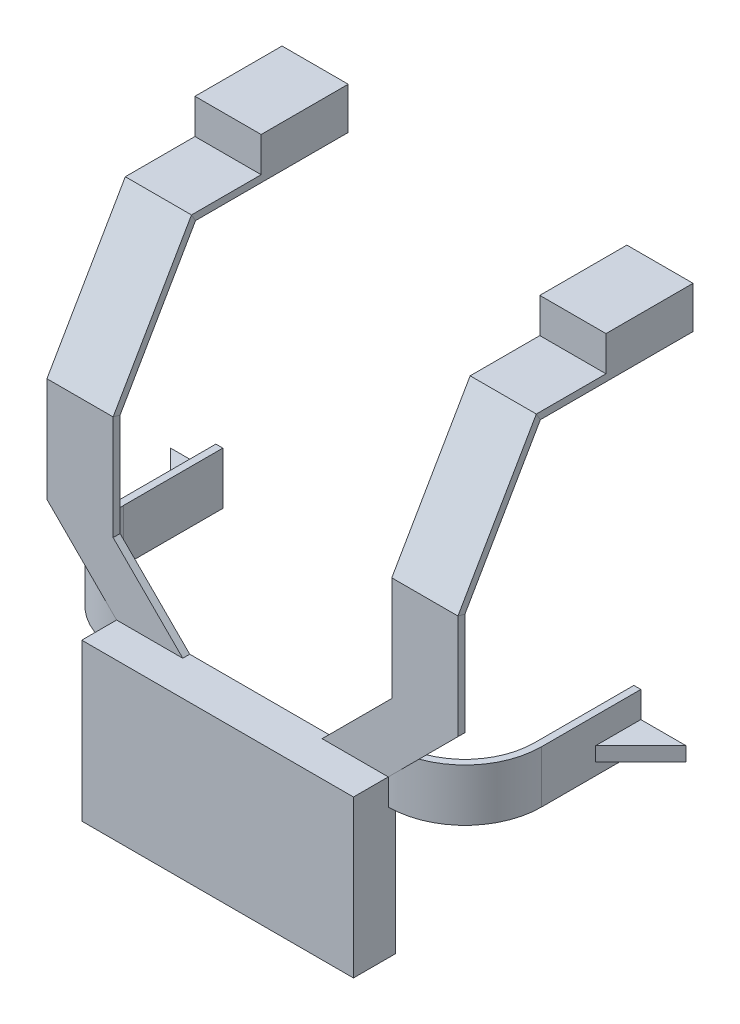
SolidWorks part; units mm, degrees
ref_plane "Front" through (0, 0, 0) normal (0, 0, 1) x (1, 0, 0)
ref_plane "Top" through (0, 0, 0) normal (0, 1, 0) x (1, 0, 0)
ref_plane "Right" through (0, 0, 0) normal (1, 0, 0) x (0, 0, -1)
sketch "草图1" plane through (0, 0, 0) normal (0, 0, 1) x (1, 0, 0)
  line L1 (0, 0) -> (0, -101.6526) construction
  line L2 (-40, 0) -> (40, 0)
  line L4 (-78, 0) -> (-78, 50)
  line L5 (-40, 50) -> (40, 50)
  line L6 (78, 0) -> (78, 50)
  line L8 (-78, 0) -> (-78, -160)
  line L9 (-78, -160) -> (-40, -160)
  line L10 (-40, 0) -> (-40, -160)
  line L12 (78, 0) -> (78, -160)
  line L13 (78, -160) -> (40, -160)
  line L14 (40, 0) -> (40, -160)
  line L15 (-143.4043, 90) -> (126.5484, 90) construction
  line L16 (-78, 50) -> (-118, 90)
  line L17 (-118, 90) -> (-80, 90)
  line L18 (-80, 90) -> (-40, 50)
  line L19 (78, 50) -> (118, 90)
  line L20 (118, 90) -> (80, 90)
  line L21 (80, 90) -> (40, 50)
  dimension "D1" = 156
  dimension "D2" = 78
  dimension "D3" = 50
  dimension "D4" = 160
  dimension "D5" = 38
  dimension "D6" = 38
  dimension "D7" = 40
  dimension "D8" = 38
  dimension "D9" = 38
extrude "凸台-拉伸1" add sketch "草图1" along normal blind 4
sketch "草图11" plane through (0, 0, 4) normal (0, 0, 1) x (1, 0, 0)
  line L0 (78, -160) -> (78, 50) construction
  line L1 (-78, 50) -> (78, 50)
  line L2 (-78, 50) -> (-78, -40)
  line L3 (-78, -40) -> (78, -40)
  line L4 (78, 50) -> (78, -40)
  dimension "D1" = 90
extrude "凸台-拉伸2" add sketch "草图11" along normal blind 20
sketch "草图12" plane through (0, 90, 0) normal (0, 1, 0) x (1, 0, 0)
  line L1 (-118, 0) -> (-80, 0)
  line L2 (-118, 0) -> (-118, -4)
  line L3 (-118, -4) -> (-80, -4)
  line L4 (-80, 0) -> (-80, -4)
  line L5 (118, 0) -> (80, 0)
  line L6 (118, 0) -> (118, -4)
  line L7 (118, -4) -> (80, -4)
  line L8 (80, 0) -> (80, -4)
sketch "草图13" plane through (78, 0, 0) normal (1, 0, 0) x (0, 0, -1)
  line L0 (-4, 90) -> (-4, 150)
  line L3 (-4, 150) -> (41, 227.9423)
  line L4 (41, 227.9423) -> (131, 227.9423)
  dimension "D1" = 60
  dimension "D2" = 150
  dimension "D3" = 90
  dimension "D5" = 90
sweep "扫描1" add profiles "草图12" path "草图13"
sketch "草图14" plane through (0, 227.9423, 0) normal (0, 1, 0) x (1, 0, 0)
  line L0 (-80, 41) -> (-80, 131) construction
  line L1 (-118, 131) -> (-80, 131)
  line L2 (-118, 131) -> (-118, 81)
  line L3 (-118, 81) -> (-80, 81)
  line L4 (-80, 131) -> (-80, 81)
  line L5 (80, 41) -> (80, 131) construction
  line L6 (118, 131) -> (80, 131)
  line L7 (118, 131) -> (118, 81)
  line L8 (118, 81) -> (80, 81)
  line L9 (80, 131) -> (80, 81)
  dimension "D1" = 50
  dimension "D2" = 50
extrude "凸台-拉伸3" add sketch "草图14" along normal blind 20
sketch "草图16" plane through (0, 0, 0) normal (0, 0, -1) x (-1, 0, 0)
  line L0 (15.8437, -40) -> (-148.9308, -40) construction
  line L1 (40, -40) -> (-40, -40) construction
  line L3 (-110.3778, -40) -> (127.8058, -40)
  line L4 (-110.3778, -40) -> (-110.3778, -172.2953)
  line L5 (-110.3778, -172.2953) -> (127.8058, -172.2953)
  line L6 (127.8058, -40) -> (127.8058, -172.2953)
extrude "切除-拉伸1" cut sketch "草图16" against normal blind 10
sketch "草图17" plane through (0, -40, 0) normal (0, -1, 0) x (1, 0, 0)
  line L0 (0, 0) -> (0, 25.1207) construction
  line L1 (-20, 0) -> (20, 0)
  line L2 (-20, 0) -> (-20, 20)
  line L3 (-20, 20) -> (20, 20)
  line L4 (20, 0) -> (20, 20)
  dimension "D1" = 40
  dimension "D2" = 20
  dimension "D3" = 20
extrude "凸台-拉伸4" add sketch "草图17" along normal blind 4
sketch "草图21" plane through (0, -44, 0) normal (0, -1, 0) x (1, 0, 0)
  line L0 (-20, 0) -> (20, 0) construction
  circle A0 centre (0, 9.5) radius 6
  circle A1 centre (0, 9.5) radius 4
  dimension "D1" = 9.5
extrude "凸台-拉伸8" add sketch "草图21" along normal blind 4
sketch "草图28" plane through (0, 50, 0) normal (0, 1, 0) x (1, 0, 0)
  line L0 (-78, -4) -> (-78, 0) construction
  line L1 (-40, -4) -> (-80, -4) construction
  line L2 (-78, -24) -> (-78, -4) construction
  line L3 (-40, 0) -> (-80, 0) construction
  line L4 (-118, 97) -> (-118, -25.7453) construction
  line L7 (-78, 0) -> (-126.1781, 48.1781) construction
  line L8 (-122, 40) -> (-122, 97)
  line L9 (-122, 97) -> (-118, 97)
  line L10 (-118, 97) -> (-118, 40)
  line L11 (-78, -4) -> (-78, 0)
  line L12 (78, -4) -> (78, 102.1257) construction
  line L13 (-78, 40) -> (78, 40) construction
  line L14 (118, -4) -> (118, 41) construction
  line L15 (-118, 97) -> (169.0103, 97) construction
  line L16 (118, 40) -> (118, 97)
  line L17 (118, 81) -> (118, 131) construction
  line L18 (122, 40) -> (122, 97)
  line L19 (122, 97) -> (118, 97)
  line L20 (78, 0) -> (78, -4)
  arc A0 (-78, 0) -> (-118, 40) centre (-78, 40) cw
  arc A1 (-78, -4) -> (-122, 40) centre (-78, 40) cw
  arc A2 (78, -4) -> (122, 40) centre (78, 40) ccw
  arc A3 (78, 0) -> (118, 40) centre (78, 40) ccw
  point P12 (78, 0)
extrude "凸台-拉伸11" add sketch "草图28" along normal mid plane 30
sketch "草图29" plane through (0, 50, 0) normal (0, 1, 0) x (1, 0, 0)
  line L0 (122, 97) -> (148, 97)
  line L1 (148, 97) -> (122, 71)
  line L2 (122, 40) -> (122, 97) construction
  line L3 (122, 71) -> (122, 97)
  line L4 (-122, 97) -> (-148, 97)
  line L5 (-148, 97) -> (-122, 71)
  line L6 (-122, 97) -> (-122, 40) construction
  line L7 (-122, 71) -> (-122, 97)
extrude "凸台-拉伸12" add sketch "草图29" against normal blind 8
